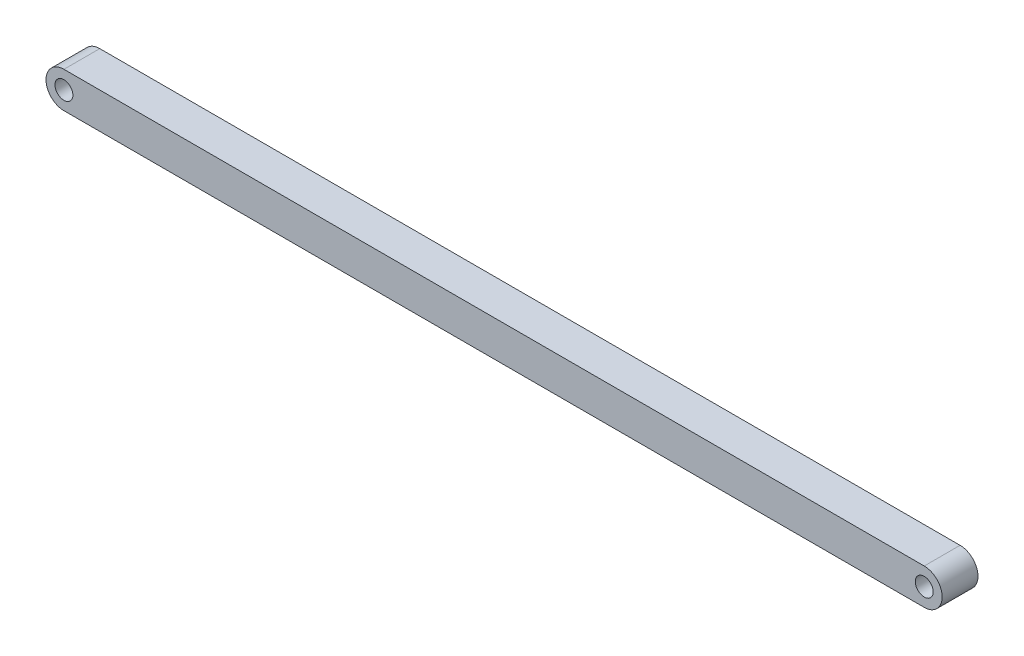
SolidWorks part; units mm, degrees
ref_plane "Front Plane" through (0, 0, 0) normal (0, 0, 1) x (1, 0, 0)
ref_plane "Top Plane" through (0, 0, 0) normal (0, 1, 0) x (1, 0, 0)
ref_plane "Right Plane" through (0, 0, 0) normal (1, 0, 0) x (0, 0, -1)
sketch "Sketch1" plane through (0, 0, 0) normal (0, 0, 1) x (1, 0, 0)
  line L0 (-304.8, 0) -> (304.8, 0) construction
  line L1 (-304.8, 12.7) -> (304.8, 12.7)
  line L2 (-304.8, -12.7) -> (304.8, -12.7)
  arc A0 (-304.8, 12.7) -> (-304.8, -12.7) centre (-304.8, 0) ccw
  arc A1 (304.8, -12.7) -> (304.8, 12.7) centre (304.8, 0) ccw
  point P3 (0, 0)
  dimension "D1" = 25.4
  dimension "D2" = 609.6
extrude "Boss-Extrude1" add sketch "Sketch1" along normal mid plane 25.4
sketch "Sketch2" plane through (0, 0, 12.7) normal (0, 0, 1) x (1, 0, 0)
  line L2 (-304.8, -12.7) -> (304.8, -12.7)
  line L3 (304.8, 12.7) -> (-304.8, 12.7)
  line L4 (-304.8, -12.7) -> (304.8, -12.7)
  line L5 (304.8, 12.7) -> (-304.8, 12.7)
  circle A0 centre (-304.8, 0) radius 6.35
  circle A1 centre (304.8, 0) radius 6.35
  arc A2 (-304.8, 12.7) -> (-304.8, -12.7) centre (-304.8, 0) ccw
  arc A3 (304.8, -12.7) -> (304.8, 12.7) centre (304.8, 0) ccw
  arc A4 (-304.8, 12.7) -> (-304.8, -12.7) centre (-304.8, 0) ccw
  arc A5 (304.8, -12.7) -> (304.8, 12.7) centre (304.8, 0) ccw
  dimension "D2" = 12.7
  dimension "D3" = 12.7
  dimension "D1" = 0
extrude "Cut-Extrude1" cut sketch "Sketch2" against normal through all contours A0 | A1
